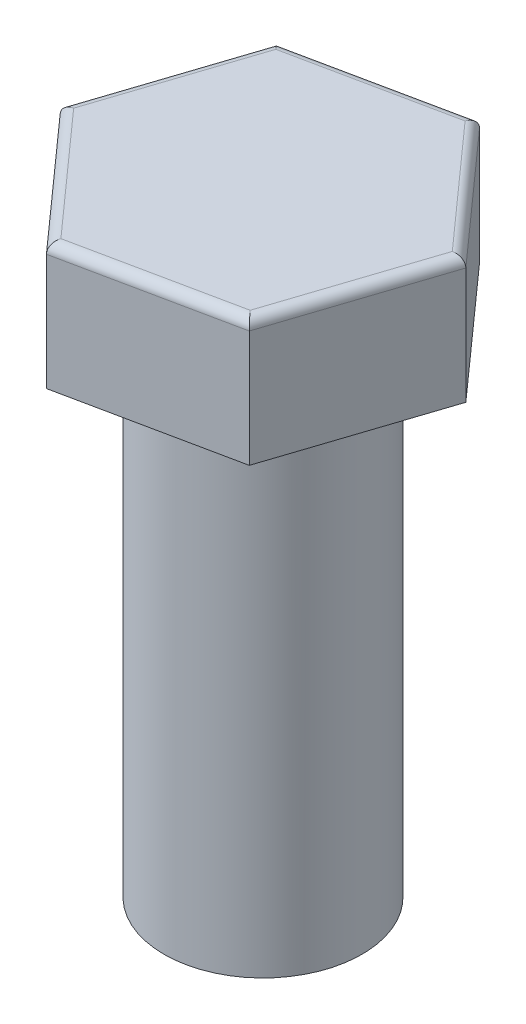
SolidWorks part; units mm, degrees
ref_plane "前视基准面" through (0, 0, 0) normal (0, 0, 1) x (1, 0, 0)
ref_plane "上视基准面" through (0, 0, 0) normal (0, 1, 0) x (1, 0, 0)
ref_plane "右视基准面" through (0, 0, 0) normal (1, 0, 0) x (0, 0, -1)
sketch "草图1" plane through (0, 0, 0) normal (0, 1, 0) x (1, 0, 0)
  line L1 (6.9214, -7.752) -> (10.1742, 2.1181)
  line L2 (10.1742, 2.1181) -> (3.2527, 9.8701)
  line L3 (3.2527, 9.8701) -> (-6.9214, 7.752)
  line L4 (-6.9214, 7.752) -> (-10.1742, -2.1181)
  line L5 (-10.1742, -2.1181) -> (-3.2527, -9.8701)
  line L6 (-3.2527, -9.8701) -> (6.9214, -7.752)
  circle A0 centre (0, 0) radius 9 construction
  dimension "D1" = 18
extrude "凸台-拉伸1" add sketch "草图1" along normal blind 7.65
sketch "草图2" plane through (0, 0, 0) normal (0, -1, 0) x (1, 0, 0)
  circle A0 centre (0, 0) radius 6
  dimension "D1" = 12
extrude "凸台-拉伸2" add sketch "草图2" along normal blind 30
cosmetic thread "装饰螺纹线1" parameters "D1"=20, "D2"=10.647
fillet "圆角1" radius 0.6 6 edges at (-1.8344, 7.65, -8.8111) (6.7134, 7.65, -5.9941) (8.5478, 7.65, 2.8169) (1.8344, 7.65, 8.8111) (-6.7134, 7.65, 5.9941) (-8.5478, 7.65, -2.8169)
